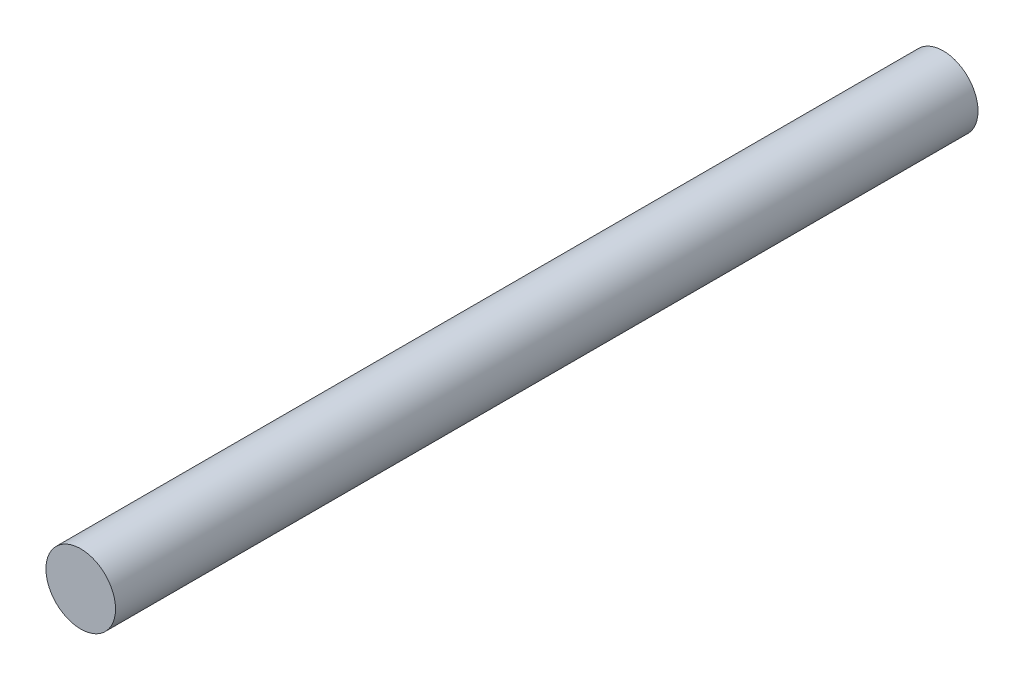
SolidWorks part; units mm, degrees
material "6061-T6 (SS)"
ref_plane "Front Plane" through (0, 0, 0) normal (0, 0, 1) x (1, 0, 0)
ref_plane "Top Plane" through (0, 0, 0) normal (0, 1, 0) x (1, 0, 0)
ref_plane "Right Plane" through (0, 0, 0) normal (1, 0, 0) x (0, 0, -1)
sketch "Sketch1" plane through (0, 0, 0) normal (0, 0, 1) x (1, 0, 0)
  circle A0 centre (0, 0) radius 2.413
  dimension "D1" = 4.826
extrude "Boss-Extrude1" add sketch "Sketch1" along normal blind 59.817
